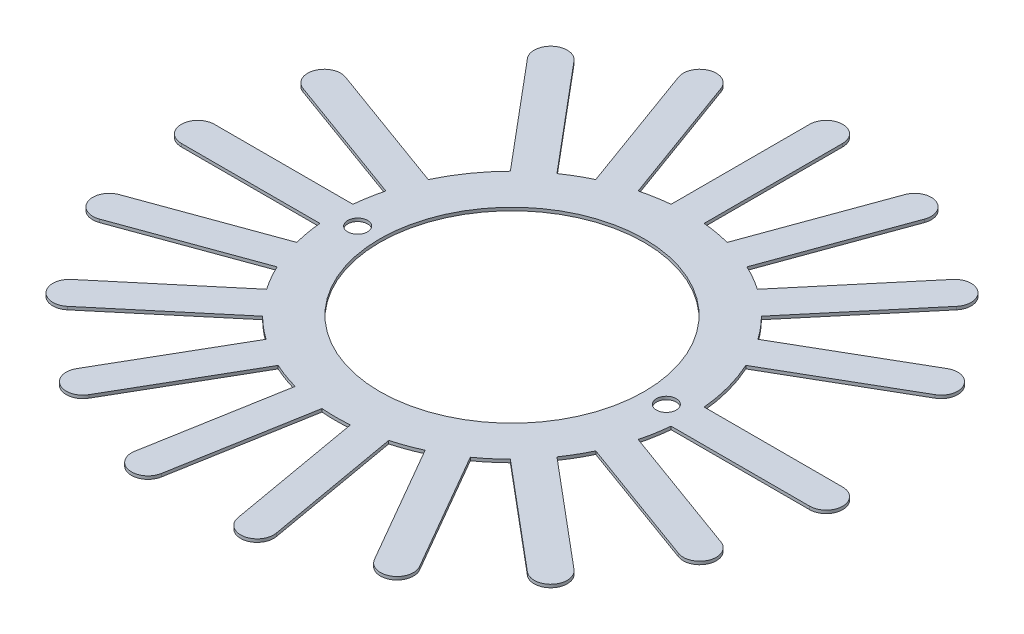
SolidWorks part; units mm, degrees
ref_plane "Front Plane" through (0, 0, 0) normal (0, 0, 1) x (1, 0, 0)
ref_plane "Top Plane" through (0, 0, 0) normal (0, 1, 0) x (1, 0, 0)
ref_plane "Right Plane" through (0, 0, 0) normal (1, 0, 0) x (0, 0, -1)
sketch "Sketch1" plane through (0, 0, 0) normal (0, 1, 0) x (1, 0, 0)
  circle A0 centre (0, 0) radius 8
  dimension "D1" = 16
extrude "Boss-Extrude2" add sketch "Sketch1" along normal blind 0.14
sketch "Sketch3" plane through (0, 0.14, 0) normal (0, 1, 0) x (1, 0, 0)
  line L0 (0, 0) -> (0, 15) construction
  line L1 (0, 0) -> (5.1303, 14.0954) construction
  line L2 (0, 0) -> (9.6418, 11.4907) construction
  line L3 (0, 0) -> (12.9904, 7.5) construction
  line L4 (0, 0) -> (15, 0) construction
  line L5 (0, 0) -> (14.0954, -5.1303) construction
  line L6 (0, 0) -> (11.4907, -9.6418) construction
  line L7 (0, 0) -> (7.5, -12.9904) construction
  line L8 (0, 0) -> (2.6047, -14.7721) construction
  line L9 (0, 0) -> (-2.6047, -14.7721) construction
  line L10 (0, 0) -> (-7.5, -12.9904) construction
  line L11 (0, 0) -> (-11.4907, -9.6418) construction
  line L12 (0, 0) -> (-14.0954, -5.1303) construction
  line L13 (0, 0) -> (-15, 0) construction
  line L14 (0, 0) -> (-14.0954, 5.1303) construction
  line L16 (7.9648, -0.75) -> (14.25, -0.75)
  line L17 (7.9648, 0.75) -> (14.25, 0.75)
  arc A0 (14.25, -0.75) -> (14.25, 0.75) centre (14.25, 0) ccw
  circle A1 centre (0, 0) radius 15 construction
  circle A2 centre (0, 0) radius 8 construction
  arc A4 (7.9648, -0.75) -> (7.9648, 0.75) centre (0, 0) ccw
  point P19 (0, -0.75)
  point P20 (15, -0.75)
  point P21 (0, 0.75)
  point P22 (15, 0.75)
  point P27 (0.375, -0.6495)
  point P28 (13.3654, 6.8505)
  point P29 (-0.375, 0.6495)
  point P30 (12.6154, 8.1495)
  dimension "D13" = 1.5
  dimension "D16" = 30
  dimension "D1" = 30
  dimension "D2" = 50
  dimension "D3" = 70
  dimension "D4" = 20
  dimension "D5" = 40
  dimension "D6" = 60
  dimension "D7" = 80
  dimension "D8" = 100
  dimension "D9" = 120
  dimension "D10" = 140
  dimension "D11" = 160
  dimension "D12" = 20
extrude "Boss-Extrude3" add sketch "Sketch3" against normal up to surface (0.14 mm away) up to face at (0, 0, 8)
pattern_circular "CirPattern3" count 11 every 20 about axis through (0, 0, 0) along (0, 1, 0) of "Boss-Extrude3"
sketch "Sketch5" plane through (0, 0.14, 0) normal (0, 1, 0) x (1, 0, 0)
  line L1 (0, 0) -> (12.9904, 7.5) construction
  line L2 (0.375, -0.6495) -> (13.3654, 6.8505)
  line L3 (7.2727, 3.3329) -> (12.7159, 6.4755)
  line L4 (-0.375, 0.6495) -> (12.6154, 8.1495)
  line L5 (6.5227, 4.6319) -> (11.9659, 7.7745)
  arc A0 (7.9648, 0.75) -> (-7.2279, 3.4289) centre (0, 0) ccw construction
  arc A1 (7.2727, 3.3329) -> (6.5227, 4.6319) centre (0, 0) ccw
  arc A2 (12.7159, 6.4755) -> (11.9659, 7.7745) centre (12.3409, 7.125) ccw
  circle A3 centre (0, 0) radius 15 construction
  dimension "D1" = 0.75
  dimension "D2" = 0.75
extrude "Boss-Extrude4" add sketch "Sketch5" against normal up to surface (0.14 mm away) up to face at (-0.9423, 0, 5.3439)
pattern_circular "CirPattern4" count 6 every 20 about axis through (0, 0, 0) along (0, 1, 0) of "Boss-Extrude4"
sketch "Sketch2" plane through (0, 0.14, 0) normal (0, 1, 0) x (1, 0, 0)
  circle A0 centre (0, 0) radius 6
  dimension "D1" = 12
extrude "Cut-Extrude3" cut sketch "Sketch2" against normal up to next
hole_wizard "Ø0.9 (0.9) Diameter Hole1" positions "Sketch7" profile "Sketch6" hole size "Ø0.9" standard "DIN" end condition up to next
sketch "Sketch7" plane through (0, 0.14, 0) normal (0, 1, 0) x (1, 0, 0)
  circle A0 centre (0, 0) radius 7 construction
  point P0 (-7, 0)
  point P2 (7, 0)
  dimension "D1" = 14
sketch "Sketch6" plane through (-7, 0.14, 0) normal (1, 0, 0) x (0, 0, 1)
  line L0 (0, 0) -> (0, 0.14)
  line L1 (0, 0.14) -> (0.45, 0.14)
  line L2 (0.45, 0.14) -> (0.45, 0)
  line L5 (0.45, 0) -> (0, 0)
  line L11 (0, -6.35) -> (0, 107.95) construction
  dimension "Thru Hole Dia." = 0.9
  dimension "Thru Hole Depth" = 0.14
